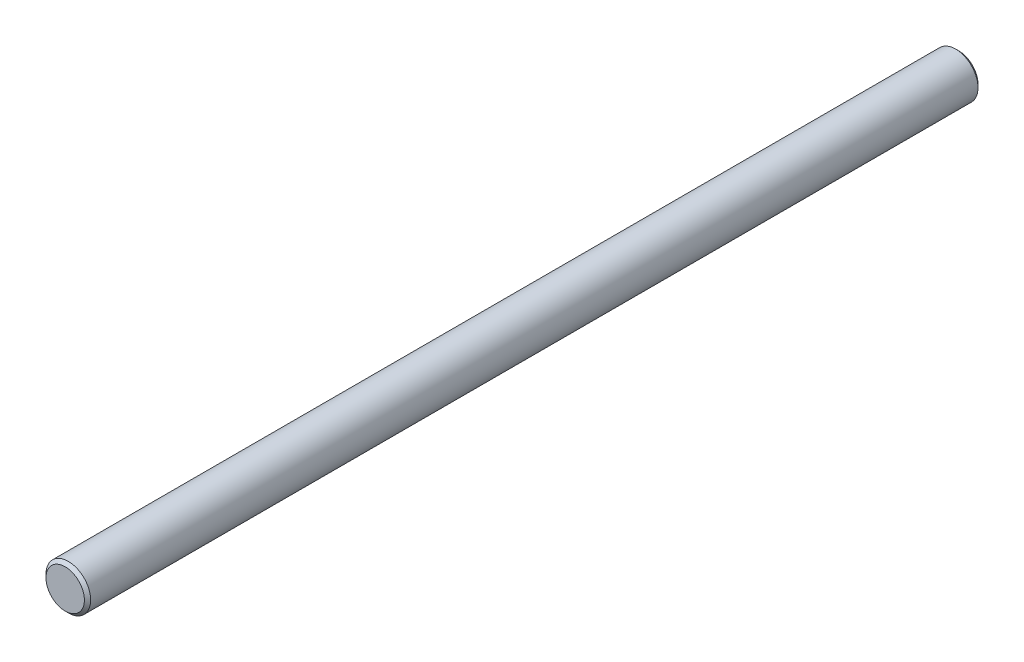
SolidWorks part; units mm, degrees
ref_plane "Front Plane" through (0, 0, 0) normal (0, 0, 1) x (1, 0, 0)
ref_plane "Top Plane" through (0, 0, 0) normal (0, 1, 0) x (1, 0, 0)
ref_plane "Right Plane" through (0, 0, 0) normal (1, 0, 0) x (0, 0, -1)
sketch "Sketch1" plane through (0, 0, 0) normal (0, 0, 1) x (1, 0, 0)
  line L0 (-2.5, 0) -> (2.5, 0) construction
  line L5 (0, 2.5) -> (0, -2.5) construction
  circle A1 centre (0, 0) radius 2.5
  point P7 (-2.5, 0)
  point P8 (2.5, 0)
  point P12 (0, -2.5)
  point P13 (0, 2.5)
  dimension "Diameter" = 5
sketch "Sketch2" plane through (0, 0, 0) normal (1, 0, 0) x (0, 0, -1)
  line L0 (-45, -2.5) -> (-45, 2.5) construction
  line L1 (50, -2.5) -> (-50, -2.5)
  line L2 (50, -2.5) -> (50, 2.5)
  line L3 (50, 2.5) -> (-50, 2.5)
  line L4 (-50, -2.5) -> (-50, 2.5)
  line L5 (50, -2.5) -> (-50, 2.5) construction
  line L6 (50, 2.5) -> (-50, -2.5) construction
  line L7 (45, -2.5) -> (45, 2.5) construction
  line L8 (-50, 2.15) -> (-49.65, 2.5) construction
  point P0 (0, 0)
  point P8 (-50, 2.5)
  point P9 (50, 2.5)
  point P14 (-45, 2.5)
  point P15 (-45, -2.5)
  point P16 (45, 2.5)
  point P17 (45, -2.5)
  point P25 (0, -2.5)
  dimension "Length" = 100
  dimension "D1" = 5
  dimension "D2" = 5
  dimension "Chamfer Typ," = 45
  dimension "D4" = 0.35
sketch "Sketch3" plane through (0, 0, 0) normal (0, 0, 1) x (1, 0, 0)
  circle A0 centre (0, 0) radius 2.5 construction
  circle A1 centre (0, 0) radius 2.5
extrude "Boss-Extrude1" add sketch "Sketch3" along normal up to vertex (50 mm away) and the other way up to vertex (50 mm away) up to point (0, 2.5, 50) other way up to point (0, 2.5, -50)
chamfer "Chamfer1" distance 0.35 angle 45 2 edges at (2.5, 0, -50) (2.5, 0, 50)
equation "\"D1@Sketch2\"=\"Diameter@Sketch1\""
equation "\"D2@Sketch2\"=\"Diameter@Sketch1\""
equation "\"D1@Chamfer1\"=\"Diameter@Sketch1\"*.07"
equation "\"D4@Sketch2\"=\"Diameter@Sketch1\"*.07"
equation "\"D2@Chamfer1\"=\"Chamfer Typ,@Sketch2\""
